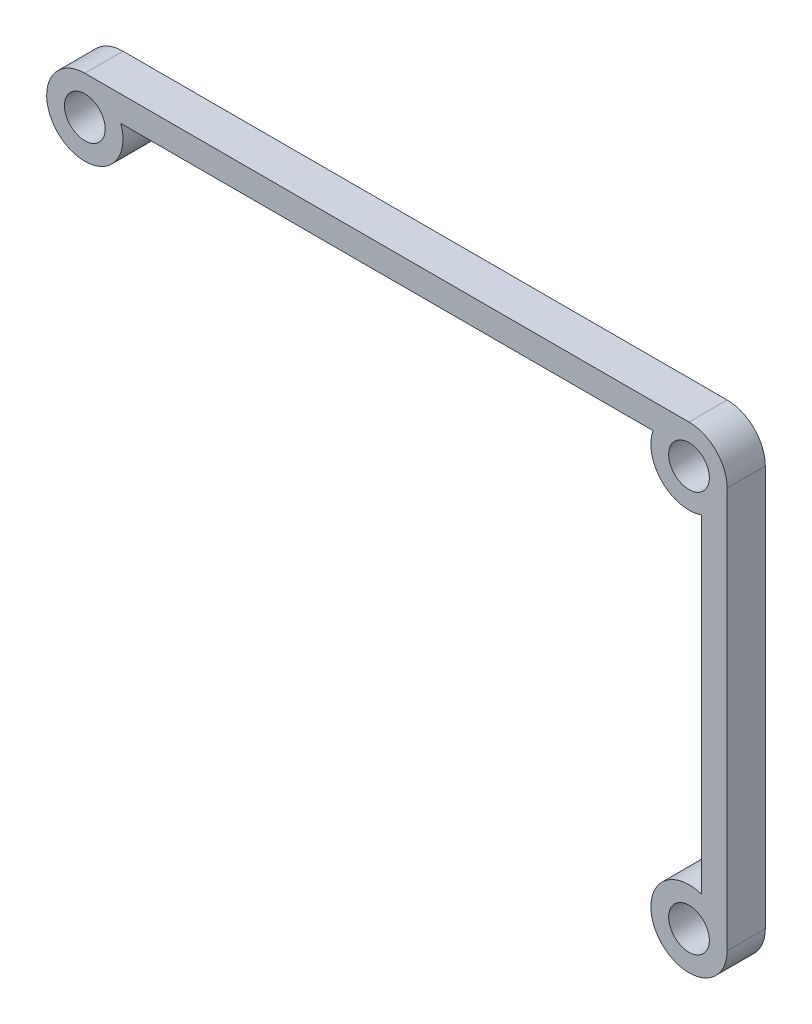
SolidWorks part; units mm, degrees
ref_plane "Plano frontal" through (0, 0, 0) normal (0, 0, 1) x (1, 0, 0)
ref_plane "Plano superior" through (0, 0, 0) normal (0, 1, 0) x (1, 0, 0)
ref_plane "Plano direito" through (0, 0, 0) normal (1, 0, 0) x (0, 0, -1)
sketch "Esboço1" plane through (0, 0, 0) normal (0, 0, 1) x (1, 0, 0)
  line L0 (0, 6.9538) -> (0, 0) construction
  line L1 (0, 0) -> (6.3156, 0) construction
  line L2 (26.75, 15.75) -> (26.75, -15.75)
  line L3 (-23.75, 18.75) -> (23.75, 18.75)
  line L4 (-20.9216, 16.75) -> (20.9216, 16.75)
  line L5 (24.75, 12.9216) -> (24.75, -12.9216)
  circle A0 centre (-23.75, 15.75) radius 1.6
  circle A1 centre (23.75, 15.75) radius 1.6
  circle A2 centre (23.75, -15.75) radius 1.6
  arc A3 (-23.75, 18.75) -> (-20.9216, 16.75) centre (-23.75, 15.75) ccw
  arc A4 (23.75, 18.75) -> (26.75, 15.75) centre (23.75, 15.75) cw
  arc A5 (24.75, -12.9216) -> (26.75, -15.75) centre (23.75, -15.75) ccw
  arc A6 (24.75, 12.9216) -> (20.9216, 16.75) centre (23.75, 15.75) cw
  dimension "D1" = 3.2
  dimension "D2" = 6
  dimension "D3" = 47.5
  dimension "D4" = 31.5
  dimension "D5" = 2
  dimension "D6" = 2
extrude "Ressalto-extrusão1" add sketch "Esboço1" along normal blind 3
equation "\"D6@Esboço1\"=\"D5@Esboço1\""
